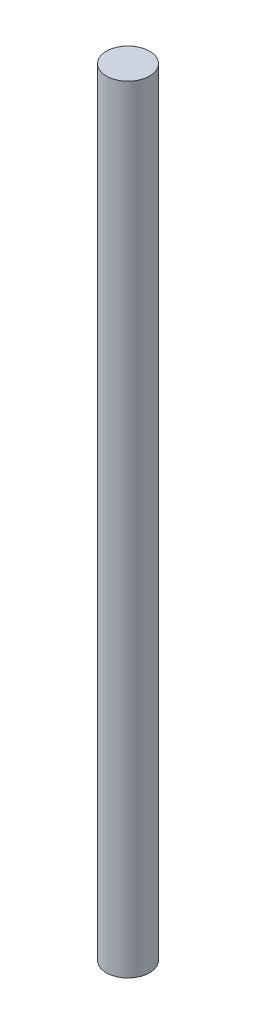
SolidWorks part; units mm, degrees
material "Acrylic (Medium-high impact)"
ref_plane "Front Plane" through (0, 0, 0) normal (0, 0, 1) x (1, 0, 0)
ref_plane "Top Plane" through (0, 0, 0) normal (0, 1, 0) x (1, 0, 0)
ref_plane "Right Plane" through (0, 0, 0) normal (1, 0, 0) x (0, 0, -1)
sketch "Sketch1" plane through (0, 0, 0) normal (0, 1, 0) x (1, 0, 0)
  circle A0 centre (0, 0) radius 3.175
  dimension "D1" = 6.35
extrude "Boss-Extrude1" add sketch "Sketch1" along normal blind 114.3 contours A0
